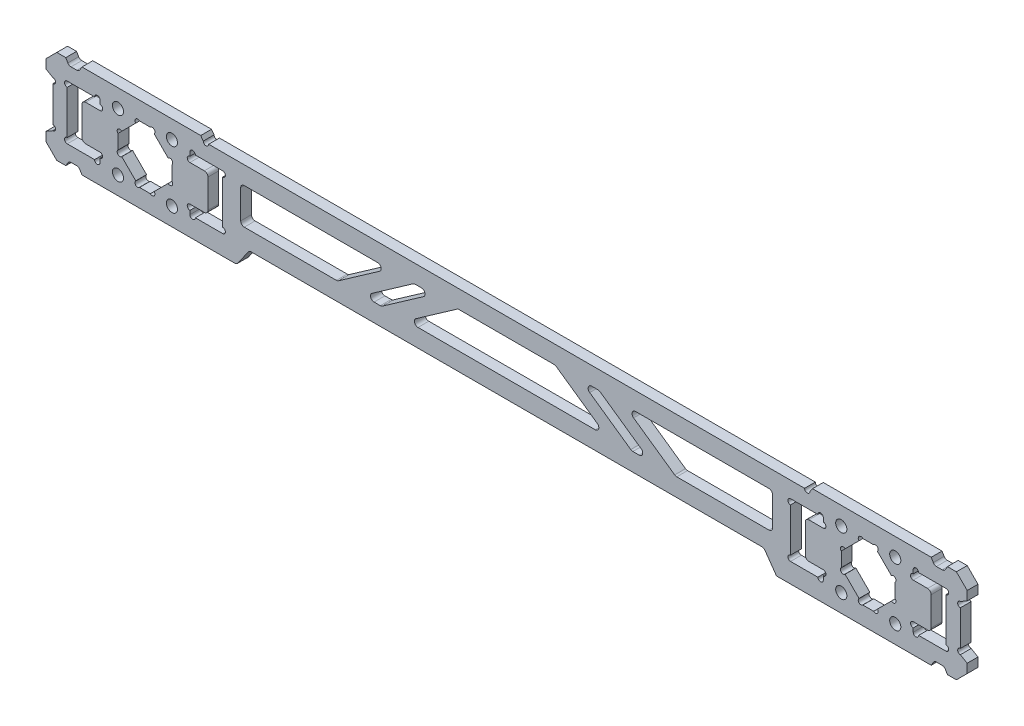
SolidWorks part; units mm, degrees
ref_plane "前视基准面" through (0, 0, 0) normal (0, 0, 1) x (1, 0, 0)
ref_plane "上视基准面" through (0, 0, 0) normal (0, 1, 0) x (1, 0, 0)
ref_plane "右视基准面" through (0, 0, 0) normal (1, 0, 0) x (0, 0, -1)
sketch "草图1" plane through (0, 0, 0) normal (0, 0, 1) x (1, 0, 0)
  line L0 (100.5, 0) -> (-100.5, 0) construction
  line L2 (-93, -8) -> (-108, -8) construction
  line L3 (-93, -8) -> (-93, 8) construction
  line L4 (-93, 8) -> (-108, 8) construction
  line L5 (-108, -8) -> (-108, 8) construction
  line L6 (-93, -8) -> (-108, 8) construction
  line L7 (-93, 8) -> (-108, -8) construction
  line L8 (108, -8) -> (93, -8) construction
  line L9 (108, -8) -> (108, 8) construction
  line L10 (108, 8) -> (93, 8) construction
  line L11 (93, -8) -> (93, 8) construction
  line L12 (108, -8) -> (93, 8) construction
  line L13 (108, 8) -> (93, -8) construction
  line L14 (128, -13) -> (-128, -13)
  line L15 (128, -13) -> (128, 13)
  line L16 (128, 13) -> (-128, 13)
  line L17 (-128, -13) -> (-128, 13)
  line L18 (128, -13) -> (-128, 13) construction
  line L19 (128, 13) -> (-128, -13) construction
  circle A0 centre (93, 8) radius 1.55
  circle A1 centre (108, 8) radius 1.55
  circle A2 centre (108, -8) radius 1.55
  circle A3 centre (93, -8) radius 1.55
  circle A4 centre (-93, 8) radius 1.55
  circle A5 centre (-93, -8) radius 1.55
  circle A6 centre (-108, -8) radius 1.55
  circle A7 centre (-108, 8) radius 1.55
  point P4 (0, 0)
  point P20 (0, 0)
  dimension "D4" = 3.1
  dimension "D1" = 15
  dimension "D2" = 16
  dimension "D3" = 186
  dimension "D5" = 5
  dimension "D6" = 20
extrude "凸台-拉伸1" add sketch "草图1" along normal mid plane 3
sketch "草图2" plane through (0, 0, 1.5) normal (0, 0, 1) x (1, 0, 0)
  line L1 (-113, 7.55) -> (-113, 5)
  line L2 (-113, 5) -> (-118, 5)
  line L3 (-118, 5) -> (-118, -5)
  line L4 (-118, -5) -> (-113, -5)
  line L5 (-113, -5) -> (-113, -7.55)
  line L6 (-113, -7.55) -> (-122.1, -7.55)
  line L7 (-122.1, -7.55) -> (-122.1, 7.55)
  line L8 (-122.1, 7.55) -> (-113, 7.55)
  line L9 (-108, 8) -> (-93, 8) construction
  line L10 (-100.5, 8) -> (-100.5, -13) construction
  line L11 (-128, -13) -> (128, -13) construction
  line L12 (-78.9, -7.55) -> (-78.9, 7.55)
  line L13 (-88, -7.55) -> (-78.9, -7.55)
  line L14 (-88, -5) -> (-88, -7.55)
  line L15 (-83, -5) -> (-88, -5)
  line L16 (-83, 5) -> (-83, -5)
  line L17 (-88, 5) -> (-83, 5)
  line L18 (-88, 7.55) -> (-88, 5)
  line L19 (-78.9, 7.55) -> (-88, 7.55)
  line L20 (-128, 13) -> (-128, -13) construction
  point P26 (-128, 0)
  point P27 (-122.1, 0)
  dimension "D1" = 15.1
  dimension "D2" = 5
  dimension "D3" = 25
  dimension "D4" = 4.1
  dimension "D5" = 10
extrude "切除-拉伸1" cut sketch "草图2" against normal through all
sketch "草图3" plane through (0, 0, 1.5) normal (0, 0, 1) x (1, 0, 0)
  line L0 (-113, 5) -> (-113, 7.55) construction
  line L1 (-113, 7.55) -> (-122.1, 7.55) construction
  line L2 (-122.1, 7.55) -> (-122.1, -7.55) construction
  line L3 (-113, -7.55) -> (-113, -5) construction
  line L4 (-122.1, -7.55) -> (-113, -7.55) construction
  line L5 (-88, 7.55) -> (-88, 5) construction
  line L6 (-78.9, 7.55) -> (-88, 7.55) construction
  line L7 (-88, -5) -> (-88, -7.55) construction
  line L8 (-88, -7.55) -> (-78.9, -7.55) construction
  line L9 (-78.9, -7.55) -> (-78.9, 7.55) construction
  circle A0 centre (-113, 5.75) radius 0.75
  circle A1 centre (-113.75, 7.55) radius 0.75
  circle A2 centre (-122.1, 6.8) radius 0.75
  circle A3 centre (-122.1, -6.8) radius 0.75
  circle A4 centre (-113, -5.75) radius 0.75
  circle A5 centre (-113.75, -7.55) radius 0.75
  circle A6 centre (-88, 5.75) radius 0.75
  circle A7 centre (-87.25, 7.55) radius 0.75
  circle A8 centre (-88, -5.75) radius 0.75
  circle A9 centre (-87.25, -7.55) radius 0.75
  circle A10 centre (-78.9, 6.8) radius 0.75
  circle A11 centre (-78.9, -6.8) radius 0.75
  dimension "D1" = 1.5
extrude "切除-拉伸2" cut sketch "草图3" against normal through all
mirror "镜向1" about plane through (0, 0, 0) normal (1, 0, 0) of "切除-拉伸1", "切除-拉伸2"
fillet "圆角1" radius 1 8 edges at (118, 5, 0) (118, -5, 0) (83, 5, 0) (83, -5, 0) (-83, -5, 0) (-83, 5, 0) (-118, -5, 0) (-118, 5, 0)
sketch "草图4" plane through (0, 0, 1.5) normal (0, 0, 1) x (1, 0, 0)
  line L0 (-128, 7.5) -> (-126.1, 6.403)
  line L1 (-128, 13) -> (-128, -13) construction
  line L2 (-126.1, 6.403) -> (-126.1, -6.403)
  line L3 (-126.1, -6.403) -> (-128, -7.5)
  line L4 (-128, -7.5) -> (-128, 7.5)
  line L5 (-122.1, 6.05) -> (-122.1, -6.05) construction
  point P7 (-128, 0)
  dimension "D1" = 15
  dimension "D2" = 4
  dimension "D3" = 60
extrude "切除-拉伸3" cut sketch "草图4" against normal through all
sketch "草图6" plane through (0, 0, 1.5) normal (0, 0, 1) x (1, 0, 0)
  line L0 (-126.1, -6.403) -> (-126.1, 6.403) construction
  circle A0 centre (-126.1, 5.653) radius 0.75
  circle A1 centre (-126.1, -5.653) radius 0.75
  dimension "D1" = 1.5
extrude "切除-拉伸5" cut sketch "草图6" against normal through all
mirror "镜向2" about plane through (0, 0, 0) normal (1, 0, 0) of "切除-拉伸5", "切除-拉伸3"
chamfer "倒角1" distance 3 angle 45 4 edges at (128, 13, 0) (128, -13, 0) (-128, -13, 0) (-128, 13, 0)
sketch "草图7" plane through (0, 0, 1.5) normal (0, 0, 1) x (1, 0, 0)
  line L5 (-122.5, 13) -> (-121.634, 11.5)
  line L6 (125, 13) -> (-125, 13) construction
  line L7 (-121.634, 11.5) -> (-118.866, 11.5)
  line L8 (-118.866, 11.5) -> (-118, 13)
  line L9 (-118, 13) -> (-122.5, 13)
  line L10 (-126.1, 0) -> (-78.9, 0) construction
  line L11 (-126.1, -4.903) -> (-126.1, 4.903) construction
  line L12 (-78.9, -6.05) -> (-78.9, 6.05) construction
  line L13 (-118.866, -11.5) -> (-118, -13)
  line L14 (-121.634, -11.5) -> (-118.866, -11.5)
  line L15 (-122.5, -13) -> (-121.634, -11.5)
  line L16 (-118, -13) -> (-122.5, -13)
  circle A0 centre (-108, 8) radius 1.55 construction
  dimension "D3" = 10
  dimension "D1" = 1.5
  dimension "D2" = 60
  dimension "D4" = 2.5
extrude "切除-拉伸6" cut sketch "草图7" against normal through all
mirror "镜向3" about plane through (0, 0, 0) normal (1, 0, 0) of "切除-拉伸6"
fillet "圆角2" radius 1 8 edges at (-118.866, 11.5, 0) (-118.866, -11.5, 0) (-121.634, -11.5, 0) (-121.634, 11.5, 0) (118.866, -11.5, 0) (121.634, -11.5, 0) (121.634, 11.5, 0) (118.866, 11.5, 0)
sketch "草图8" plane through (0, 0, 1.5) normal (0, 0, 1) x (1, 0, 0)
  line L0 (-108, 2) -> (-108, -2)
  line L1 (-102, -8) -> (-99, -8)
  line L2 (-93, -2) -> (-93, 2)
  line L3 (-99, 8) -> (-102, 8)
  line L4 (-102, 8) -> (-108, 2)
  line L5 (-93, 2) -> (-99, 8)
  line L6 (-99, -8) -> (-93, -2)
  line L7 (-108, -2) -> (-102, -8)
  point P0 (-108, 8)
  point P1 (-108, -8)
  point P5 (-93, -8)
  point P7 (-93, 8)
extrude "切除-拉伸7" cut sketch "草图8" against normal through all
sketch "草图9" plane through (0, 0, 1.5) normal (0, 0, 1) x (1, 0, 0)
  line L0 (-102, 8) -> (-108, 2) construction
  line L1 (-93, 2) -> (-99, 8) construction
  line L2 (-99, -8) -> (-93, -2) construction
  line L3 (-108, -2) -> (-102, -8) construction
  circle A0 centre (-107.4697, 2.5303) radius 0.75
  circle A1 centre (-102.5303, 7.4697) radius 0.75
  circle A2 centre (-98.4697, 7.4697) radius 0.75
  circle A3 centre (-93.5303, 2.5303) radius 0.75
  circle A4 centre (-93.5303, -2.5303) radius 0.75
  circle A5 centre (-98.4697, -7.4697) radius 0.75
  circle A6 centre (-102.5303, -7.4697) radius 0.75
  circle A7 centre (-107.4697, -2.5303) radius 0.75
  dimension "D1" = 1.5
extrude "切除-拉伸8" cut sketch "草图9" against normal through all
mirror "镜向4" about plane through (0, 0, 0) normal (1, 0, 0) of "切除-拉伸8", "切除-拉伸7"
sketch "草图10" plane through (0, 0, 1.5) normal (0, 0, 1) x (1, 0, 0)
  line L0 (-85, -13) -> (-84.2998, -12) construction
  line L1 (-118, -13) -> (118, -13) construction
  line L2 (-84.2998, -12) -> (84.2998, -12) construction
  line L3 (84.2998, -12) -> (85, -13) construction
  line L4 (85, -13) -> (-85, -13) construction
  line L5 (-78.9, 0) -> (78.9, 0) construction
  line L6 (-78.9, -6.05) -> (-78.9, 6.05) construction
  line L7 (78.9, -6.05) -> (78.9, 6.05) construction
  line L8 (84.2998, 12) -> (85, 13)
  line L9 (-85, 13) -> (-84.2998, 12)
  line L10 (85, 13) -> (-85, 13)
  line L11 (-84.2998, 12) -> (84.2998, 12)
  point P5 (0, -12)
  dimension "D1" = 1
  dimension "D2" = 55
  dimension "D3" = 170
extrude "切除-拉伸9" cut sketch "草图10" against normal through all
sketch "草图11" plane through (0, 0, 1.5) normal (0, 0, 1) x (1, 0, 0)
  line L1 (-84.2998, 12) -> (84.2998, 12) construction
  circle A0 centre (-83.5498, 12) radius 0.75
  circle A1 centre (83.5498, 12) radius 0.75
  dimension "D1" = 1.5
extrude "切除-拉伸10" cut sketch "草图11" against normal through all
sketch "草图13" plane through (0, 0, -1.5) normal (0, 0, -1) x (-1, 0, 0)
  line L0 (-75, -13) -> (-71.499, -8)
  line L1 (118, -13) -> (-118, -13) construction
  line L2 (-71.499, -8) -> (71.499, -8)
  line L3 (71.499, -8) -> (75, -13)
  line L4 (75, -13) -> (-75, -13)
  point P4 (0, -8)
  dimension "D1" = 55
  dimension "D2" = 5
  dimension "D3" = 150
extrude "切除-拉伸11" cut sketch "草图13" against normal through all
sketch "草图14" plane through (0, 0, 1.5) normal (0, 0, 1) x (1, 0, 0)
  line L0 (-73.9, 7) -> (-73.9, -3)
  line L1 (-73.9, -3) -> (-46.9738, -3)
  line L2 (-46.9738, -3) -> (-32.6923, 7)
  line L3 (-32.6923, 7) -> (-73.9, 7)
  line L4 (-25.7185, 7) -> (-40, -3)
  line L5 (-40, -3) -> (-34.7697, -3)
  line L6 (0, -3) -> (0, 7) construction
  line L7 (25.7185, 7) -> (20.4882, 7)
  line L8 (-82.7998, 12) -> (82.7998, 12) construction
  line L9 (-71.499, -8) -> (71.499, -8) construction
  line L10 (-78.9, -6.05) -> (-78.9, 6.05) construction
  line L11 (25.7185, 7) -> (40, -3)
  line L12 (46.9738, -3) -> (32.6923, 7)
  line L13 (73.9, -3) -> (46.9738, -3)
  line L14 (73.9, 7) -> (73.9, -3)
  line L15 (32.6923, 7) -> (73.9, 7)
  line L16 (-20.4882, 7) -> (-34.7697, -3)
  line L17 (-13.5144, 7) -> (-27.7959, -3)
  line L18 (13.5144, 7) -> (27.7959, -3)
  line L19 (20.4882, 7) -> (34.7697, -3)
  line L20 (-20.4882, 7) -> (-25.7185, 7)
  line L21 (-27.7959, -3) -> (27.7959, -3)
  line L22 (13.5144, 7) -> (-13.5144, 7)
  line L23 (34.7697, -3) -> (40, -3)
  dimension "D1" = 5
  dimension "D2" = 5
  dimension "D3" = 5
  dimension "D4" = 40
  dimension "D5" = 35
  dimension "D6" = 4
  dimension "D7" = 4
  dimension "D8" = 3
extrude "切除-拉伸12" cut sketch "草图14" against normal through all
fillet "圆角3" radius 1 23 edges at (-73.9, -3, 0) (-73.9, 7, 0) (-46.9738, -3, 0) (-32.6923, 7, 0) (-40, -3, 0) (25.7185, 7, 0) (46.9738, -3, 0) (32.6923, 7, 0) (73.9, 7, 0) (73.9, -3, 0) (-75, -13, 0) (-71.499, -8, 0) (71.499, -8, 0) (40, -3, 0) (34.7697, -3, 0) (20.4882, 7, 0) (27.7959, -3, 0) (13.5144, 7, 0) (-27.7959, -3, 0) (-13.5144, 7, 0) (-25.7185, 7, 0) (-34.7697, -3, 0) (-20.4882, 7, 0)
